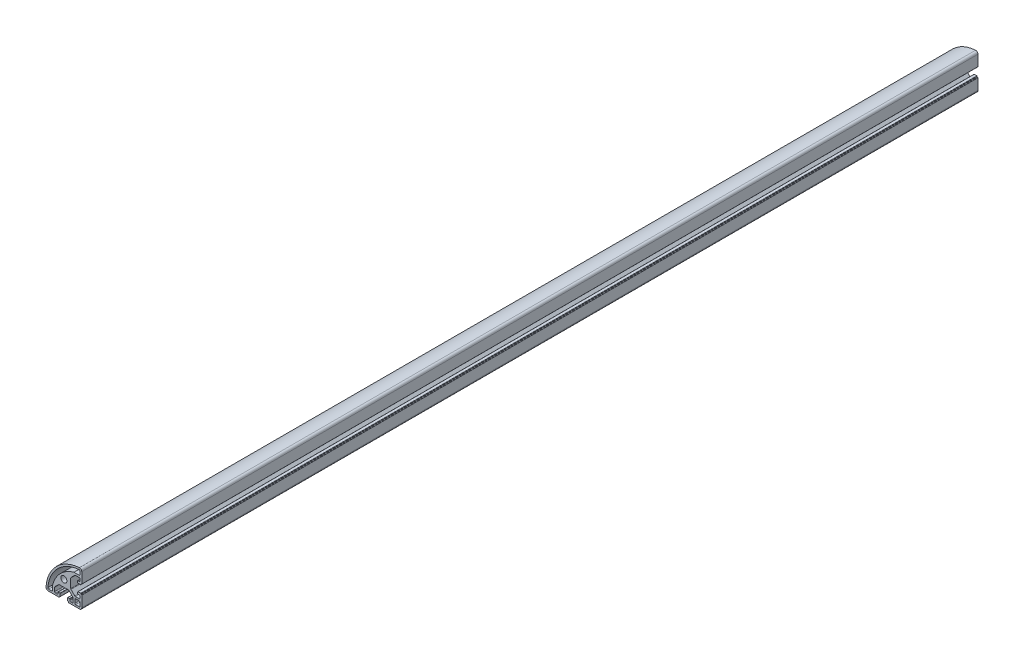
SolidWorks part; units mm, degrees
material "6063 T5"
ref_plane "Спереди" through (0, 0, 0) normal (0, 0, 1) x (1, 0, 0)
ref_plane "Сверху" through (0, 0, 0) normal (0, 1, 0) x (1, 0, 0)
ref_plane "Справа" through (0, 0, 0) normal (1, 0, 0) x (0, 0, -1)
sketch "Эскиз1" plane through (0, 0, 0) normal (0, 0, 1) x (1, 0, 0)
  line L0 (10.25, -20) -> (17.5, -20)
  line L1 (20, -17.5) -> (20, -10.25)
  line L2 (20, 17.4166) -> (20, 10.25)
  line L3 (-17.4166, -20) -> (-10.25, -20)
  line L4 (18, 16.8782) -> (18, 13.4473)
  line L5 (17, 12.4473) -> (11.2747, 12.4473)
  line L6 (-16.8782, -18) -> (-13.4473, -18)
  line L7 (-12.4473, -17) -> (-12.4473, -11.2747)
  line L8 (-19.9864, 20.9431) -> (20.0136, 20.9431) construction
  line L10 (13.2, -12.2) -> (17, -12.2)
  line L11 (12.2, -13.2) -> (12.2, -17)
  line L12 (13.2, -18) -> (17, -18)
  line L13 (18, -13.2) -> (18, -17)
  arc A0 (17.3333, 19.911) -> (-19.911, -17.3333) centre (20, -20) ccw
  circle A1 centre (0, 0) radius 3.4
  arc A2 (-17.8749, -16.9189) -> (16.9189, 17.8749) centre (20, -20) cw
  arc A3 (11.2747, 12.4473) -> (-12.4473, -11.2747) centre (20, -20) ccw
  arc A4 (12.2, -17) -> (13.2, -18) centre (13.2, -17) ccw
  arc A5 (17, -18) -> (18, -17) centre (17, -17) ccw
  arc A6 (17, -12.2) -> (18, -13.2) centre (17, -13.2) cw
  arc A7 (13.2, -12.2) -> (12.2, -13.2) centre (13.2, -13.2) ccw
  arc A8 (17.3333, 19.911) -> (20, 17.4166) centre (17.5, 17.4166) cw
  arc A9 (-19.911, -17.3333) -> (-17.4166, -20) centre (-17.4166, -17.5) ccw
  arc A10 (17.5, -20) -> (20, -17.5) centre (17.5, -17.5) ccw
  arc A11 (16.9189, 17.8749) -> (18, 16.8782) centre (17, 16.8782) cw
  arc A12 (18, 13.4473) -> (17, 12.4473) centre (17, 13.4473) cw
  arc A13 (-13.4473, -18) -> (-12.4473, -17) centre (-13.4473, -17) ccw
  arc A14 (-17.8749, -16.9189) -> (-16.8782, -18) centre (-16.8782, -17) ccw
  point P28 (18, -12.2)
  point P31 (12.2, -12.2)
  point P48 (-12.4473, -18)
  point P51 (-17.9473, -18)
  line B0 (20, -10.25) -> (20, -5.4)
  line B1 (19.7, -5.1) -> (19.3, -5.1)
  line B2 (19, -4.8) -> (19, -4.4)
  line B3 (18.7, -4.1) -> (15.8, -4.1)
  line B4 (15.5, -4.4) -> (15.5, -6.3)
  line B5 (15.8, -6.6) -> (17, -6.6)
  line B6 (18, -7.6) -> (18, -9.25)
  line B7 (17, -10.25) -> (12.8642, -10.25)
  line B8 (12.1571, -9.9571) -> (7.9929, -5.7929)
  line B9 (7.7, -5.0858) -> (7.7, 5.0858)
  line B10 (7.7, 0) -> (20, 0) construction
  line B11 (12.1571, 9.9571) -> (7.9929, 5.7929)
  line B12 (17, 10.25) -> (12.8642, 10.25)
  line B13 (18, 7.6) -> (18, 9.25)
  line B14 (15.8, 6.6) -> (17, 6.6)
  line B15 (15.5, 4.4) -> (15.5, 6.3)
  line B16 (18.7, 4.1) -> (15.8, 4.1)
  line B17 (19, 4.8) -> (19, 4.4)
  line B18 (19.7, 5.1) -> (19.3, 5.1)
  line B19 (20, 10.25) -> (20, 5.4)
  arc B20 (15.5, -6.3) -> (15.8, -6.6) centre (15.8, -6.3) ccw
  arc B21 (15.8, -4.1) -> (15.5, -4.4) centre (15.8, -4.4) ccw
  arc B22 (19, -4.4) -> (18.7, -4.1) centre (18.7, -4.4) ccw
  arc B23 (19.3, -5.1) -> (19, -4.8) centre (19.3, -4.8) cw
  arc B24 (20, -5.4) -> (19.7, -5.1) centre (19.7, -5.4) ccw
  arc B25 (7.9929, -5.7929) -> (7.7, -5.0858) centre (8.7, -5.0858) cw
  arc B26 (12.8642, -10.25) -> (12.1571, -9.9571) centre (12.8642, -9.25) cw
  arc B27 (18, -9.25) -> (17, -10.25) centre (17, -9.25) cw
  arc B28 (17, -6.6) -> (18, -7.6) centre (17, -7.6) cw
  arc B29 (17, 6.6) -> (18, 7.6) centre (17, 7.6) ccw
  arc B30 (18, 9.25) -> (17, 10.25) centre (17, 9.25) ccw
  arc B31 (12.8642, 10.25) -> (12.1571, 9.9571) centre (12.8642, 9.25) ccw
  arc B32 (7.9929, 5.7929) -> (7.7, 5.0858) centre (8.7, 5.0858) ccw
  arc B33 (20, 5.4) -> (19.7, 5.1) centre (19.7, 5.4) cw
  arc B34 (19.3, 5.1) -> (19, 4.8) centre (19.3, 4.8) ccw
  arc B35 (19, 4.4) -> (18.7, 4.1) centre (18.7, 4.4) cw
  arc B36 (15.8, 4.1) -> (15.5, 4.4) centre (15.8, 4.4) cw
  arc B37 (15.5, 6.3) -> (15.8, 6.6) centre (15.8, 6.3) cw
  line B38 (-10.25, -20) -> (-5.4, -20)
  line B39 (-5.1, -19.7) -> (-5.1, -19.3)
  line B40 (-4.8, -19) -> (-4.4, -19)
  line B41 (-4.1, -18.7) -> (-4.1, -15.8)
  line B42 (-4.4, -15.5) -> (-6.3, -15.5)
  line B43 (-6.6, -15.8) -> (-6.6, -17)
  line B44 (-7.6, -18) -> (-9.25, -18)
  line B45 (-10.25, -17) -> (-10.25, -12.8642)
  line B46 (-9.9571, -12.1571) -> (-5.7929, -7.9929)
  line B47 (-5.0858, -7.7) -> (5.0858, -7.7)
  line B48 (0, -7.7) -> (0, -20) construction
  line B49 (9.9571, -12.1571) -> (5.7929, -7.9929)
  line B50 (10.25, -17) -> (10.25, -12.8642)
  line B51 (7.6, -18) -> (9.25, -18)
  line B52 (6.6, -15.8) -> (6.6, -17)
  line B53 (4.4, -15.5) -> (6.3, -15.5)
  line B54 (4.1, -18.7) -> (4.1, -15.8)
  line B55 (4.8, -19) -> (4.4, -19)
  line B56 (5.1, -19.7) -> (5.1, -19.3)
  line B57 (10.25, -20) -> (5.4, -20)
  arc B58 (-6.3, -15.5) -> (-6.6, -15.8) centre (-6.3, -15.8) ccw
  arc B59 (-4.1, -15.8) -> (-4.4, -15.5) centre (-4.4, -15.8) ccw
  arc B60 (-4.4, -19) -> (-4.1, -18.7) centre (-4.4, -18.7) ccw
  arc B61 (-5.1, -19.3) -> (-4.8, -19) centre (-4.8, -19.3) cw
  arc B62 (-5.4, -20) -> (-5.1, -19.7) centre (-5.4, -19.7) ccw
  arc B63 (-5.7929, -7.9929) -> (-5.0858, -7.7) centre (-5.0858, -8.7) cw
  arc B64 (-10.25, -12.8642) -> (-9.9571, -12.1571) centre (-9.25, -12.8642) cw
  arc B65 (-9.25, -18) -> (-10.25, -17) centre (-9.25, -17) cw
  arc B66 (-6.6, -17) -> (-7.6, -18) centre (-7.6, -17) cw
  arc B67 (6.6, -17) -> (7.6, -18) centre (7.6, -17) ccw
  arc B68 (9.25, -18) -> (10.25, -17) centre (9.25, -17) ccw
  arc B69 (10.25, -12.8642) -> (9.9571, -12.1571) centre (9.25, -12.8642) ccw
  arc B70 (5.7929, -7.9929) -> (5.0858, -7.7) centre (5.0858, -8.7) ccw
  arc B71 (5.4, -20) -> (5.1, -19.7) centre (5.4, -19.7) cw
  arc B72 (5.1, -19.3) -> (4.8, -19) centre (4.8, -19.3) ccw
  arc B73 (4.4, -19) -> (4.1, -18.7) centre (4.4, -18.7) cw
  arc B74 (4.1, -15.8) -> (4.4, -15.5) centre (4.4, -15.8) cw
  arc B75 (6.3, -15.5) -> (6.6, -15.8) centre (6.3, -15.8) cw
  dimension "D3" = 40
  dimension "D4" = 6.8
  dimension "D9" = 1
  dimension "D10" = 2.5
  dimension "D13" = 38
  dimension "D15" = 33.6
  dimension "D16" = 1
  dimension "D1" = 20
  dimension "D2" = 20
  dimension "D5" = 40
  dimension "D6" = 2
  dimension "D7" = 2
  dimension "D8" = 5.8
  dimension "D11" = 2
  dimension "D12" = 2
  dimension "D14" = 5.5
sketch_block_instance "8B(20,5PL)-2"
sketch_block "8B(20,5PL)" parameters "D7"=0.3, "D8"=1, "D1"=12.3, "D2"=4.5, "D3"=8.2, "D4"=20.5, "D5"=10.2, "D6"=135, "D9"=0.4, "D10"=1.65, "D11"=10.7577, "D12"=1.2
sketch_block_instance "8B(20,5PL)-3"
extrude "Бобышка-Вытянуть1" add sketch "Эскиз1" along normal blind 1000 contours B75 B53 B74 B54 B73 B55 B72 B56 B71 B57 L0 A10 L1 B0 B24 B1 B23 B2 B22 B3 B21 B4 B20 B5 B28 B6 B27 B7 B26 B8 B25 B9 B32 B11 B31 B12 B30 B13 B29 B14 B37 B15 B36 B16 B35 B17 B34 B18 B33 B19 L2
